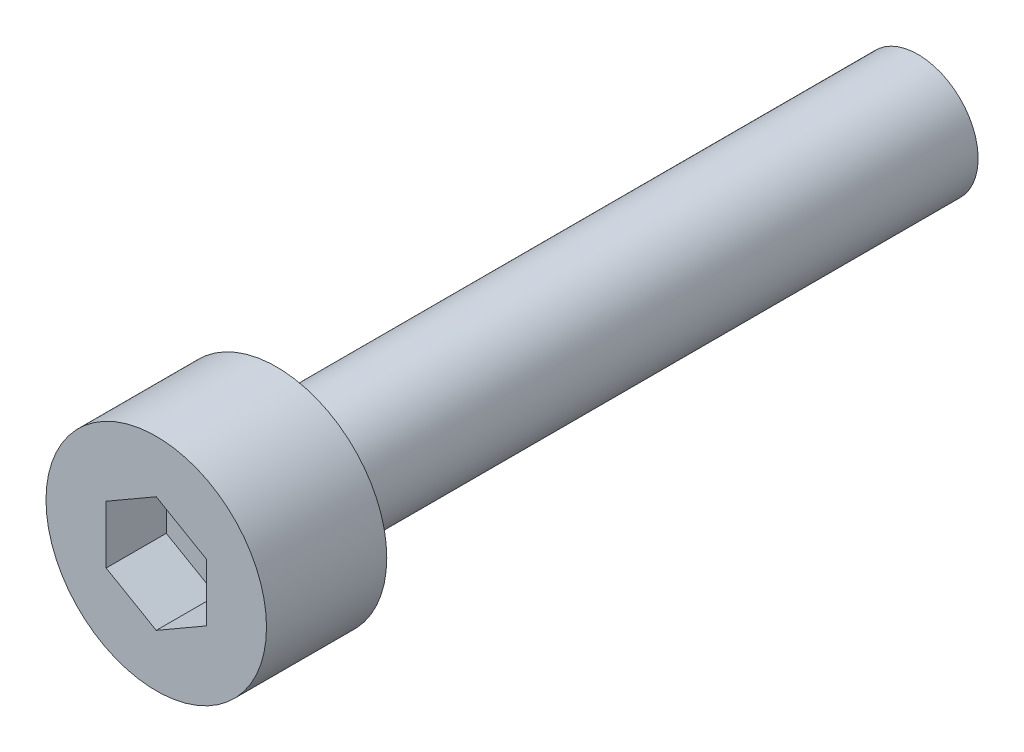
SolidWorks part; units mm, degrees
material "灰铸铁"
ref_plane "前视基准面" through (0, 0, 0) normal (0, 0, 1) x (1, 0, 0)
ref_plane "上视基准面" through (0, 0, 0) normal (0, 1, 0) x (1, 0, 0)
ref_plane "右视基准面" through (0, 0, 0) normal (1, 0, 0) x (0, 0, -1)
sketch "草图1" plane through (0, 0, 0) normal (0, 0, 1) x (1, 0, 0)
  circle A0 centre (0, 0) radius 2.75
  dimension "D1" = 5.5
extrude "凸台-拉伸1" add sketch "草图1" along normal blind 3
sketch "草图2" plane through (0, 0, 3) normal (0, 0, 1) x (1, 0, 0)
  line L1 (0, -1.4434) -> (1.25, -0.7217)
  line L2 (1.25, -0.7217) -> (1.25, 0.7217)
  line L3 (1.25, 0.7217) -> (0, 1.4434)
  line L4 (0, 1.4434) -> (-1.25, 0.7217)
  line L5 (-1.25, 0.7217) -> (-1.25, -0.7217)
  line L6 (-1.25, -0.7217) -> (0, -1.4434)
  circle A0 centre (0, 0) radius 1.25 construction
  dimension "D1" = 2.5
extrude "切除-拉伸1" cut sketch "草图2" against normal blind 1.5
sketch "草图3" plane through (0, 0, 0) normal (0, 0, -1) x (-1, 0, 0)
  circle A0 centre (0, 0) radius 1.5
extrude "凸台-拉伸2" add sketch "草图3" along normal blind 16
